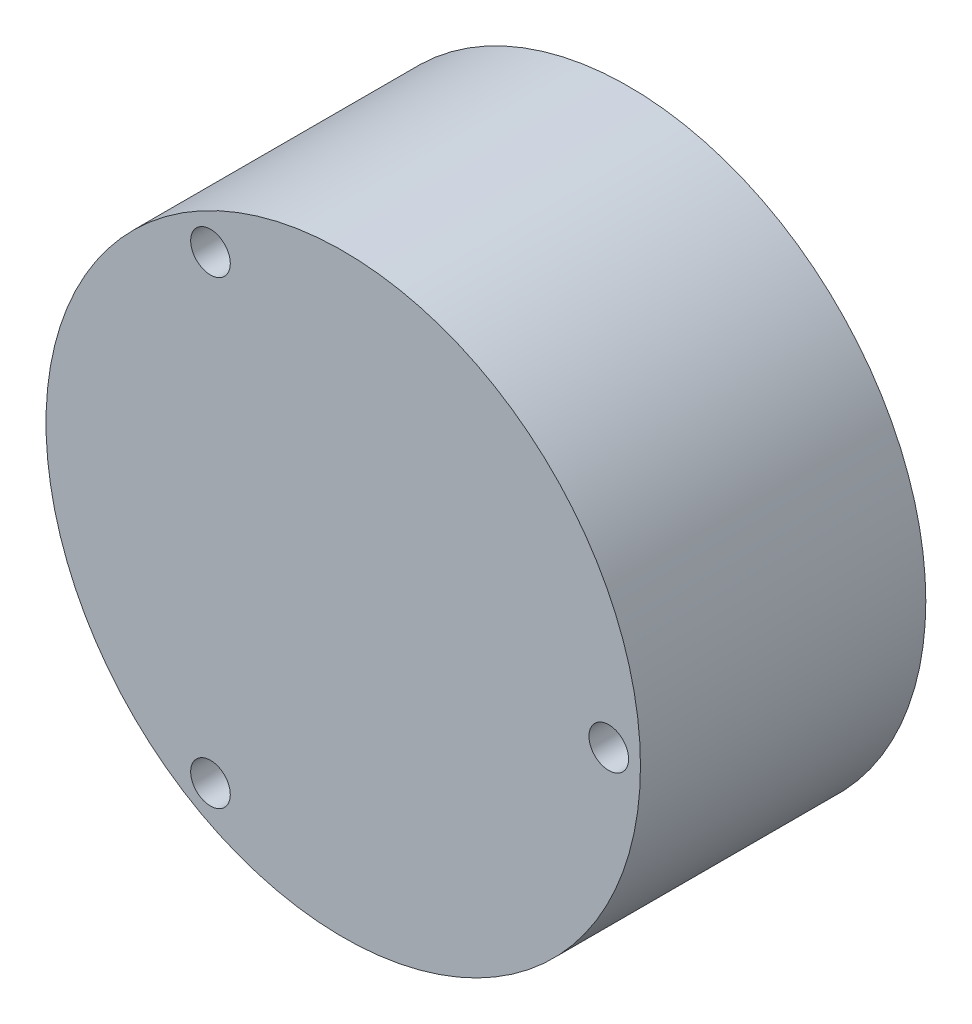
SolidWorks part; units mm, degrees
ref_plane "前视基准面" through (0, 0, 0) normal (0, 0, 1) x (1, 0, 0)
ref_plane "上视基准面" through (0, 0, 0) normal (0, 1, 0) x (1, 0, 0)
ref_plane "右视基准面" through (0, 0, 0) normal (1, 0, 0) x (0, 0, -1)
sketch "草图1" plane through (0, 0, 0) normal (0, 0, 1) x (1, 0, 0)
  circle A0 centre (0, 0) radius 18.75
  circle A1 centre (0, 0) radius 14.5
extrude "凸台-拉伸1" add sketch "草图1" along normal blind 16
sketch "草图2" plane through (0, 0, 16) normal (0, 0, 1) x (1, 0, 0)
  circle A2 centre (16.625, 0) radius 1.25
  circle A3 centre (-8.3125, -14.3977) radius 1.25
  circle A4 centre (-8.3125, 14.3977) radius 1.25
  point P8 (0, 0)
  dimension "D1" = 3
extrude "切除-拉伸1" cut sketch "草图2" against normal blind 18
sketch "草图3" plane through (0, 0, 16) normal (0, 0, 1) x (1, 0, 0)
  arc A2 (-7.1426, -15.7567) -> (17.217, -1.6927) centre (0, 0) ccw
  arc A3 (-7.1426, -15.7567) -> (-10.0744, -14.064) centre (-8.3125, -14.3977) ccw
  arc A4 (-10.0744, 14.064) -> (-7.1426, 15.7567) centre (-8.3125, 14.3977) ccw
  arc A5 (17.217, 1.6927) -> (17.217, -1.6927) centre (16.625, 0) ccw
  arc A6 (17.217, 1.6927) -> (-7.1426, 15.7567) centre (0, 0) ccw
  arc A7 (-10.0744, 14.064) -> (-10.0744, -14.064) centre (0, 0) ccw
  point P17 (0, 0)
  dimension "D1" = 3
extrude "切除-拉伸2" cut sketch "草图3" against normal blind 18
sketch "草图4" plane through (0, 0, 16) normal (0, 0, 1) x (1, 0, 0)
  circle A0 centre (0, 0) radius 18.75
extrude "凸台-拉伸2" add sketch "草图4" along normal blind 2
sketch "草图6" plane through (0, 0, 0) normal (0, 0, -1) x (-1, 0, 0)
  circle A0 centre (8.3125, -14.3977) radius 1.25 construction
  circle A1 centre (-16.625, 0) radius 1.25 construction
  circle A2 centre (8.3125, 14.3977) radius 1.25 construction
  circle A3 centre (8.3125, -14.3977) radius 1.25
  circle A4 centre (-16.625, 0) radius 1.25
  circle A5 centre (8.3125, 14.3977) radius 1.25
extrude "凸台-拉伸3" add sketch "草图6" against normal up to surface (16 mm away) up to face at (0, 0, 16)
sketch "草图7" plane through (0, 0, 0) normal (0, 0, -1) x (-1, 0, 0)
  circle A1 centre (8.375, 14.5059) radius 1.25
  circle A2 centre (8.375, -14.5059) radius 1.25
  circle A3 centre (-16.75, 0) radius 1.25
  point P9 (0, 0)
extrude "切除-拉伸3" cut sketch "草图7" against normal blind 20
